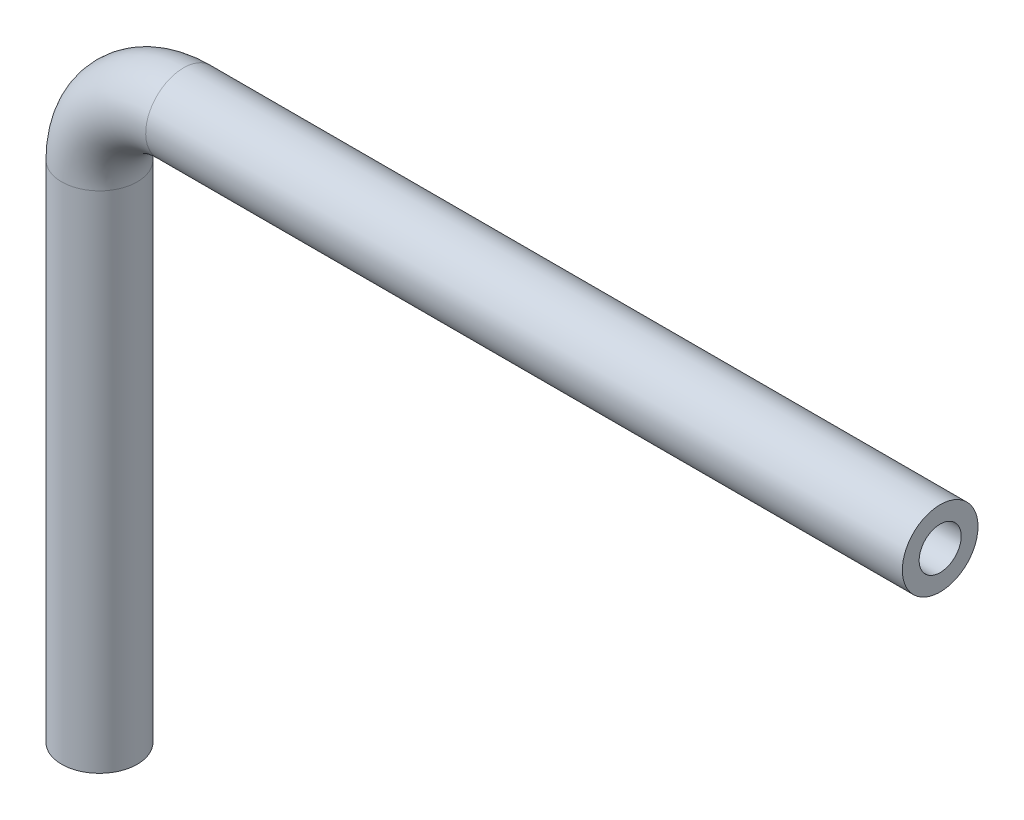
SolidWorks part; units mm, degrees
ref_plane "Front Plane" through (0, 0, 0) normal (0, 0, 1) x (1, 0, 0)
ref_plane "Top Plane" through (0, 0, 0) normal (0, 1, 0) x (1, 0, 0)
ref_plane "Right Plane" through (0, 0, 0) normal (1, 0, 0) x (0, 0, -1)
ref_plane "Plane1" through (1, 0, 0) normal (1, 0, 0) x (0, 0, -1)
sketch "Sketch1" plane through (1, 0, 0) normal (1, 0, 0) x (0, 0, -1)
  line L0 (-0.4, 6) -> (0.4, 6) construction
  circle A0 centre (0, 7) radius 0.45
  circle A1 centre (0, 7) radius 0.25
  dimension "D2" = 0.9
  dimension "D1" = 1
revolve "Revolve1" add sketch "Sketch1" angle 90 about L0
ref_plane "Plane2" through (0, 6, 0) normal (0, -1, 0) x (-1, 0, 0)
sketch "Sketch6" plane through (0, 6, 0) normal (0, -1, 0) x (-1, 0, 0)
  circle A0 centre (0, 0) radius 0.45
  dimension "D1" = 0.9
extrude "Boss-Extrude1" add sketch "Sketch6" along normal blind 6
sketch "Sketch11" plane through (1, 0, 0) normal (1, 0, 0) x (0, 0, -1)
  circle A0 centre (0, 7) radius 0.45
  dimension "D1" = 0.9
extrude "Boss-Extrude2" add sketch "Sketch11" along normal blind 9
ref_plane "Plane3" through (0, 0, 0) normal (0, 0, -1) x (-1, 0, 0)
sketch "Sketch17" plane through (0, 0, 0) normal (0, 0, -1) x (-1, 0, 0)
  line L0 (-10, 7.25) -> (-10, 7)
  line L1 (-10, 7) -> (-1, 7)
  line L2 (-1, 7) -> (-1, 7.25)
  line L3 (-1, 7.25) -> (-10, 7.25)
  line L4 (-10, 7) -> (-1, 7) construction
revolve "Cut-Revolve1" cut sketch "Sketch17" angle 360 about L1
sketch "Sketch19" plane through (0, 0, 0) normal (0, 0, 1) x (1, 0, 0)
  line L0 (0.25, 6) -> (0, 6)
  line L1 (0, 6) -> (0, 0)
  line L2 (0, 0) -> (0.25, 0)
  line L3 (0.25, 0) -> (0.25, 6)
  line L4 (0, 6) -> (0, 0) construction
revolve "Cut-Revolve2" cut sketch "Sketch19" angle 360 about L1
